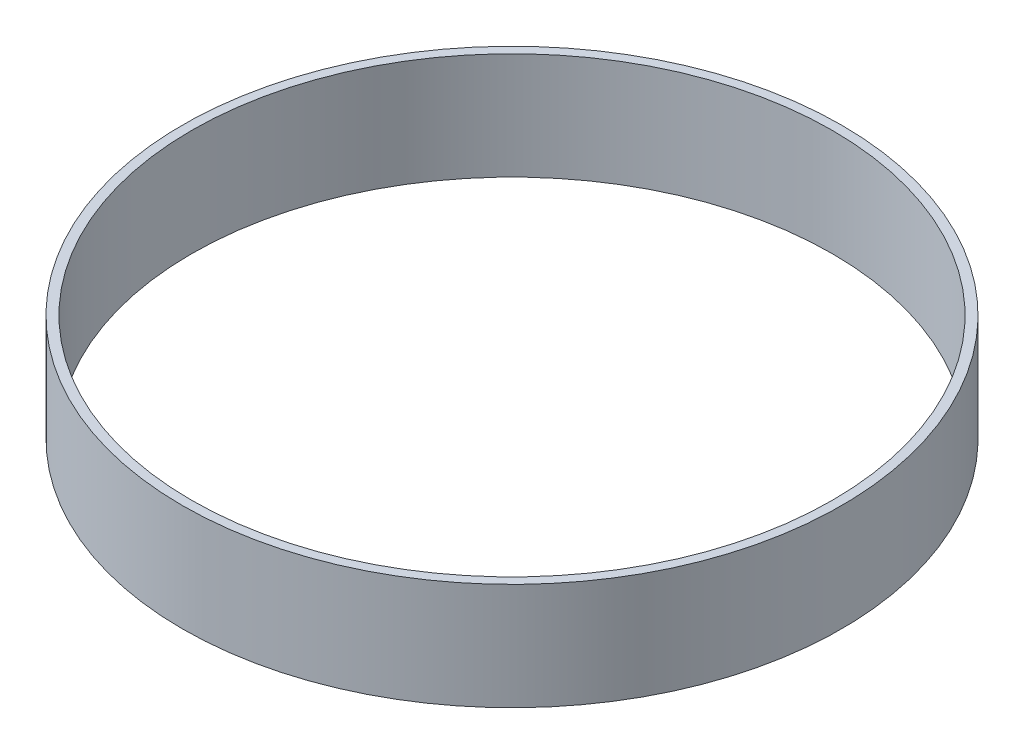
SolidWorks part; units mm, degrees
material "A-Glass Fiber"
ref_plane "Front Plane" through (0, 0, 0) normal (0, 0, 1) x (1, 0, 0)
ref_plane "Top Plane" through (0, 0, 0) normal (0, 1, 0) x (1, 0, 0)
ref_plane "Right Plane" through (0, 0, 0) normal (1, 0, 0) x (0, 0, -1)
sketch "Sketch1" plane through (0, 0, 0) normal (0, 1, 0) x (1, 0, 0)
  circle A0 centre (0, 0) radius 76.1746
  circle A1 centre (0, 0) radius 78.359
  dimension "D1" = 152.3492
  dimension "D2" = 156.718
extrude "Boss-Extrude1" add sketch "Sketch1" along normal blind 25.4
equation "\"Mid_Tube_Length\" = 1in"
equation "\"D1@Boss-Extrude1\"=\"Mid_Tube_Length\""
equation "\"Bodytube_OD\" = 6.17in"
equation "\"Bodytube_ID\" = 5.998in"
equation "\"D1@Sketch1\"=\"Bodytube_ID\""
equation "\"D2@Sketch1\"=\"Bodytube_OD\""
